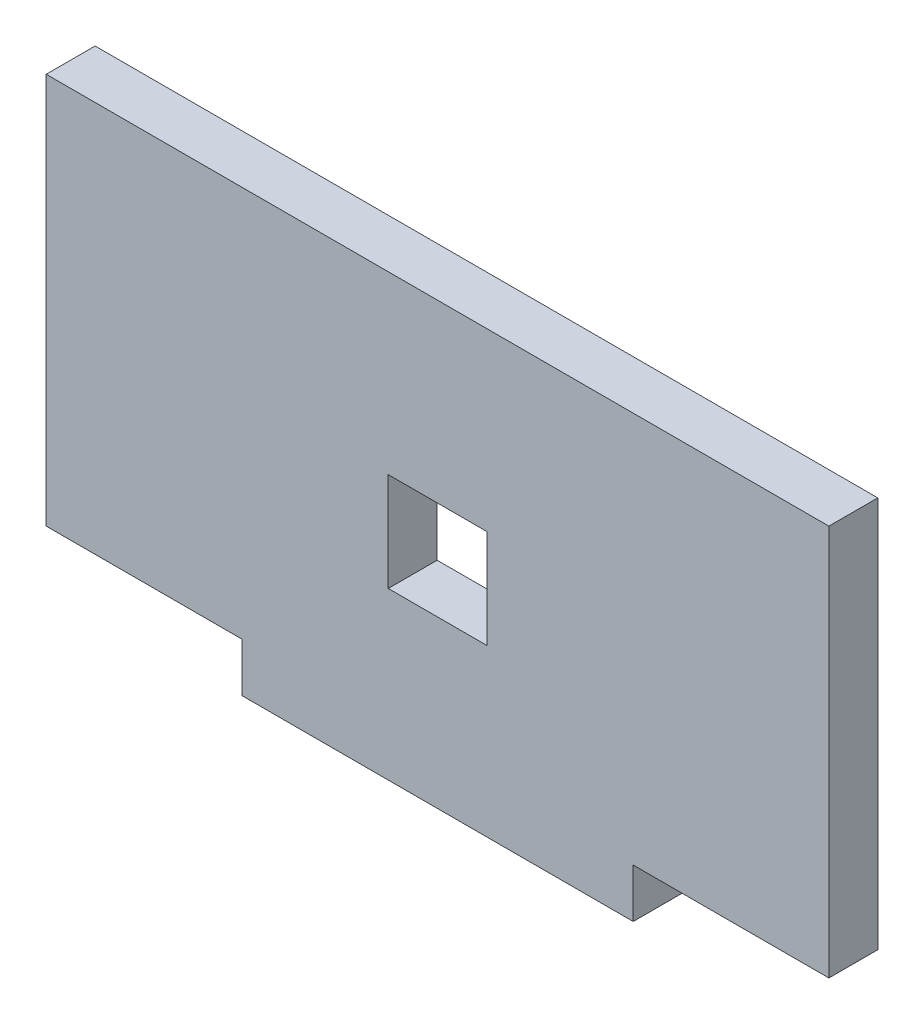
SolidWorks part; units mm, degrees
ref_plane "Front Plane" through (0, 0, 0) normal (0, 0, 1) x (1, 0, 0)
ref_plane "Top Plane" through (0, 0, 0) normal (0, 1, 0) x (1, 0, 0)
ref_plane "Right Plane" through (0, 0, 0) normal (1, 0, 0) x (0, 0, -1)
sketch "Sketch1" plane through (0, 0, 0) normal (0, 0, 1) x (1, 0, 0)
  line L1 (-25.4, -14.2875) -> (25.4, -14.2875)
  line L2 (-25.4, -14.2875) -> (-25.4, 14.2875)
  line L3 (-25.4, 14.2875) -> (25.4, 14.2875)
  line L4 (25.4, -14.2875) -> (25.4, 14.2875)
  line L5 (-25.4, -14.2875) -> (25.4, 14.2875) construction
  line L6 (-25.4, 14.2875) -> (25.4, -14.2875) construction
  point P0 (0, 0)
  dimension "D1" = 50.8
  dimension "D2" = 28.575
extrude "Boss-Extrude1" add sketch "Sketch1" along normal blind 3.175
sketch "Sketch2" plane through (0, 0, 3.175) normal (0, 0, 1) x (1, 0, 0)
  line L0 (0, -14.2875) -> (0, -0.3175) construction
  line L1 (-25.4, -14.2875) -> (-12.7, -14.2875)
  line L2 (-25.4, -14.2875) -> (-25.4, -11.1125)
  line L3 (-25.4, -11.1125) -> (-12.7, -11.1125)
  line L4 (-12.7, -14.2875) -> (-12.7, -11.1125)
  line L5 (25.4, -14.2875) -> (12.7, -14.2875)
  line L6 (25.4, -14.2875) -> (25.4, -11.1125)
  line L7 (25.4, -11.1125) -> (12.7, -11.1125)
  line L8 (12.7, -14.2875) -> (12.7, -11.1125)
  line L9 (-25.4, -14.2875) -> (25.4, -14.2875) construction
  line L11 (-3.2004, -3.5179) -> (3.2004, -3.5179)
  line L12 (-3.2004, -3.5179) -> (-3.2004, 2.8829)
  line L13 (-3.2004, 2.8829) -> (3.2004, 2.8829)
  line L14 (3.2004, -3.5179) -> (3.2004, 2.8829)
  line L15 (-3.2004, -3.5179) -> (3.2004, 2.8829) construction
  line L16 (-3.2004, 2.8829) -> (3.2004, -3.5179) construction
  dimension "D4" = 13.97
  dimension "D5" = 6.4008
  dimension "D1" = 12.7
  dimension "D2" = 12.7
  dimension "D3" = 3.175
  dimension "D6" = 6.4008
extrude "Cut-Extrude1" cut sketch "Sketch2" against normal blind 3.175
